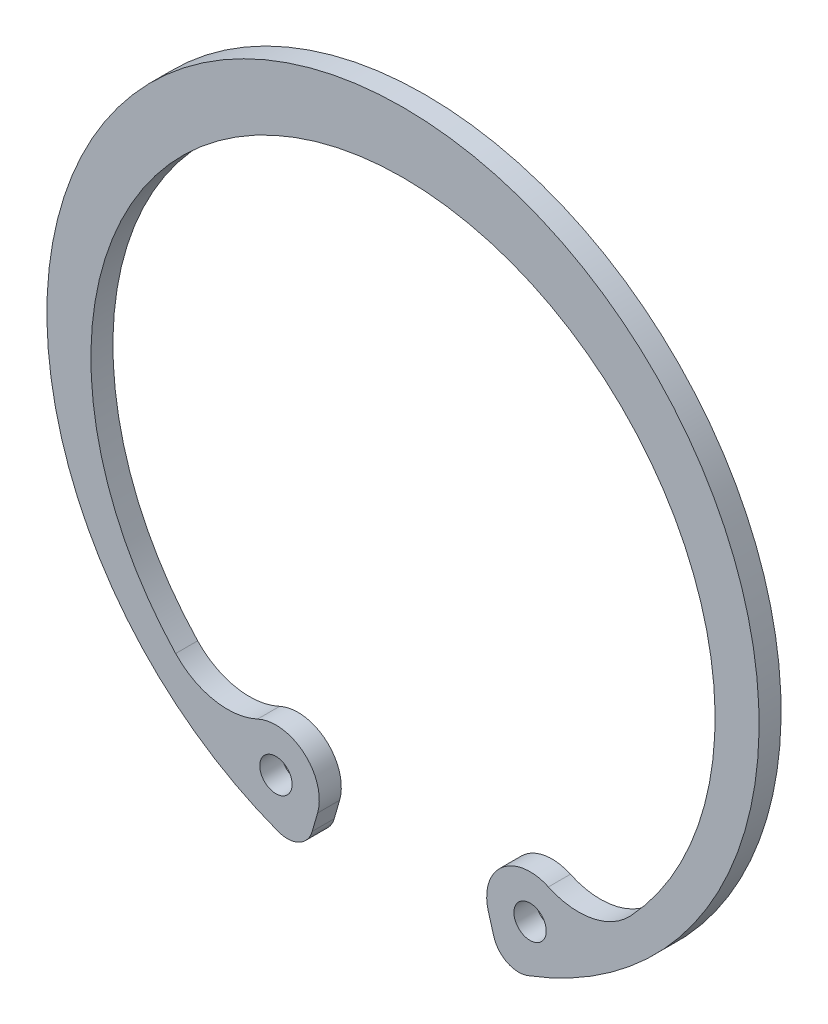
SolidWorks part; units mm, degrees
material "AISI 1020"
ref_plane "Спереди" through (0, 0, 0) normal (0, 0, 1) x (1, 0, 0)
ref_plane "Сверху" through (0, 0, 0) normal (0, 1, 0) x (1, 0, 0)
ref_plane "Справа" through (0, 0, 0) normal (1, 0, 0) x (0, 0, -1)
sketch "Эскиз1" plane through (0, 0, 0) normal (0, 0, 1) x (1, 0, 0)
  line L0 (0, -1000) -> (0, 49000) construction
  line L1 (0, 0) -> (11.35, -21.9941) construction
  line L2 (8.1925, -23.1133) -> (8.6939, -24.5281)
  line L3 (0, 23.4) -> (49.4, 23.4) construction
  arc A0 (11.3897, -25.6882) -> (0, 28.1) centre (0, 0) ccw
  circle A2 centre (11.35, -21.9941) radius 1.25
  arc A3 (12.5818, -18.8788) -> (8.1925, -23.1133) centre (11.35, -21.9941) ccw
  arc A4 (12.5818, -18.8788) -> (18.7878, -17.3346) centre (14.6043, -13.7641) ccw
  arc A5 (8.6939, -24.5281) -> (11.3897, -25.6882) centre (10.579, -23.8599) ccw
  arc A6 (18.7878, -17.3346) -> (0, 23.4) centre (0, -1.3) ccw
  dimension "_d2" = 56.2
  dimension "_d4" = 2.5
  dimension "_r1" = 5.5
  dimension "_r2" = 2
  dimension "D1" = 24.7
  dimension "_e" = 1.3
  dimension "_a" = 6.7
  dimension "_l" = 16
  dimension "_d3" = 49.4
sketch "Эскиз2" plane through (0, 0, 0) normal (0, 0, 1) x (1, 0, 0)
  line L0 (0, -201000) -> (0, 249000) construction
  line L1 (-7.0114, -24.4392) -> (-6.5948, -22.9971)
  line L2 (8.1925, -23.1133) -> (8.6939, -24.5281) construction
  line L3 (0, 0) -> (11.3897, -25.6882) construction
  line L4 (0, 0) -> (-9.6334, -25.7575) construction
  line L5 (8.6939, -24.5281) -> (11.3897, -25.6882) construction
  line L6 (-9.6334, -25.7575) -> (-7.0114, -24.4392) construction
  line L7 (12.5818, -18.8788) -> (8.1925, -23.1133) construction
  line L8 (-11.228, -19.0309) -> (-6.5948, -22.9971) construction
  line L9 (0, 27.5) -> (0, 29.2) construction
  circle A0 centre (0, 0) radius 27.5 construction
  circle A1 centre (0, 0) radius 26 construction
  circle A2 centre (0, 0) radius 18.8 construction
  arc A3 (0, 27.5) -> (-9.6334, -25.7575) centre (0, 0) ccw
  arc A4 (0, 22.8) -> (-17.5572, -17.8134) centre (0, -1.3017) ccw
  arc A5 (-9.6334, -25.7575) -> (-7.0114, -24.4392) centre (-8.9328, -23.8842) ccw
  arc A6 (-6.5948, -22.9971) -> (-11.228, -19.0309) centre (-9.8133, -22.0675) ccw
  arc A7 (8.6939, -24.5281) -> (11.3897, -25.6882) centre (10.579, -23.8599) ccw construction
  arc A8 (12.5818, -18.8788) -> (8.1925, -23.1133) centre (11.35, -21.9941) ccw construction
  arc A9 (-17.5572, -17.8134) -> (-11.228, -19.0309) centre (-13.5507, -14.0454) ccw
  circle A10 centre (-9.8133, -22.0675) radius 1.25
  circle A11 centre (11.35, -21.9941) radius 1.25 construction
  arc A13 (12.5818, -18.8788) -> (18.7878, -17.3346) centre (14.6043, -13.7641) ccw construction
  dimension "_D" = 52
  dimension "_d1" = 55
  dimension "_DD" = 37.6
  dimension "_b" = 4.7
  dimension "D1" = 156.088
  dimension "D2" = 28.1
  dimension "D3" = 159.494
  dimension "_s" = 1.7
sketch "Эскиз3" plane through (0, 0, 0) normal (0, 0, 1) x (1, 0, 0)
  line L0 (-7.0114, -24.4392) -> (-6.5948, -22.9971) construction
  line L1 (-7.0114, -24.4392) -> (-6.5948, -22.9971)
  line L2 (0, -1000) -> (0, 49000) construction
  line L3 (0, -1000.0733) -> (0, 48999.9267) construction
  line L4 (7.0114, -24.4392) -> (6.5948, -22.9971)
  arc A0 (0, 22.8) -> (-17.5572, -17.8134) centre (0, -1.3017) ccw construction
  arc A1 (-17.5572, -17.8134) -> (-11.228, -19.0309) centre (-13.5507, -14.0454) ccw construction
  arc A2 (-6.5948, -22.9971) -> (-11.228, -19.0309) centre (-9.8133, -22.0675) ccw construction
  arc A3 (-9.6334, -25.7575) -> (-7.0114, -24.4392) centre (-8.9328, -23.8842) ccw construction
  arc A4 (0, 27.5) -> (-9.6334, -25.7575) centre (0, 0) ccw construction
  arc A5 (17.5572, -17.8134) -> (-17.5572, -17.8134) centre (0, -1.3017) ccw
  arc A6 (-17.5572, -17.8134) -> (-11.228, -19.0309) centre (-13.5507, -14.0454) ccw
  arc A7 (-6.5948, -22.9971) -> (-11.228, -19.0309) centre (-9.8133, -22.0675) ccw
  arc A8 (-9.6334, -25.7575) -> (-7.0114, -24.4392) centre (-8.9328, -23.8842) ccw
  arc A9 (9.6334, -25.7575) -> (-9.6334, -25.7575) centre (0, 0) ccw
  circle A10 centre (-9.8133, -22.0675) radius 1.25 construction
  circle A11 centre (-9.8133, -22.0675) radius 1.25
  circle A12 centre (9.8133, -22.0675) radius 1.25
  arc A13 (17.5572, -17.8134) -> (11.228, -19.0309) centre (13.5507, -14.0454) cw
  arc A14 (6.5948, -22.9971) -> (11.228, -19.0309) centre (9.8133, -22.0675) cw
  arc A15 (9.6334, -25.7575) -> (7.0114, -24.4392) centre (8.9328, -23.8842) cw
extrude "Бобышка-Вытянуть1" add sketch "Эскиз3" along normal blind 1.7
equation "\"D1@Эскиз1\"=\"_d3@Эскиз1\"/2"
equation "\"D3@Эскиз2\"=(\"D2@Эскиз2\"*2*\"D1@Эскиз2\"/360)/(\"_d1@Эскиз2\"/360)"
equation "\"D1@Бобышка-Вытянуть1\"= \"_s@Эскиз2\""
